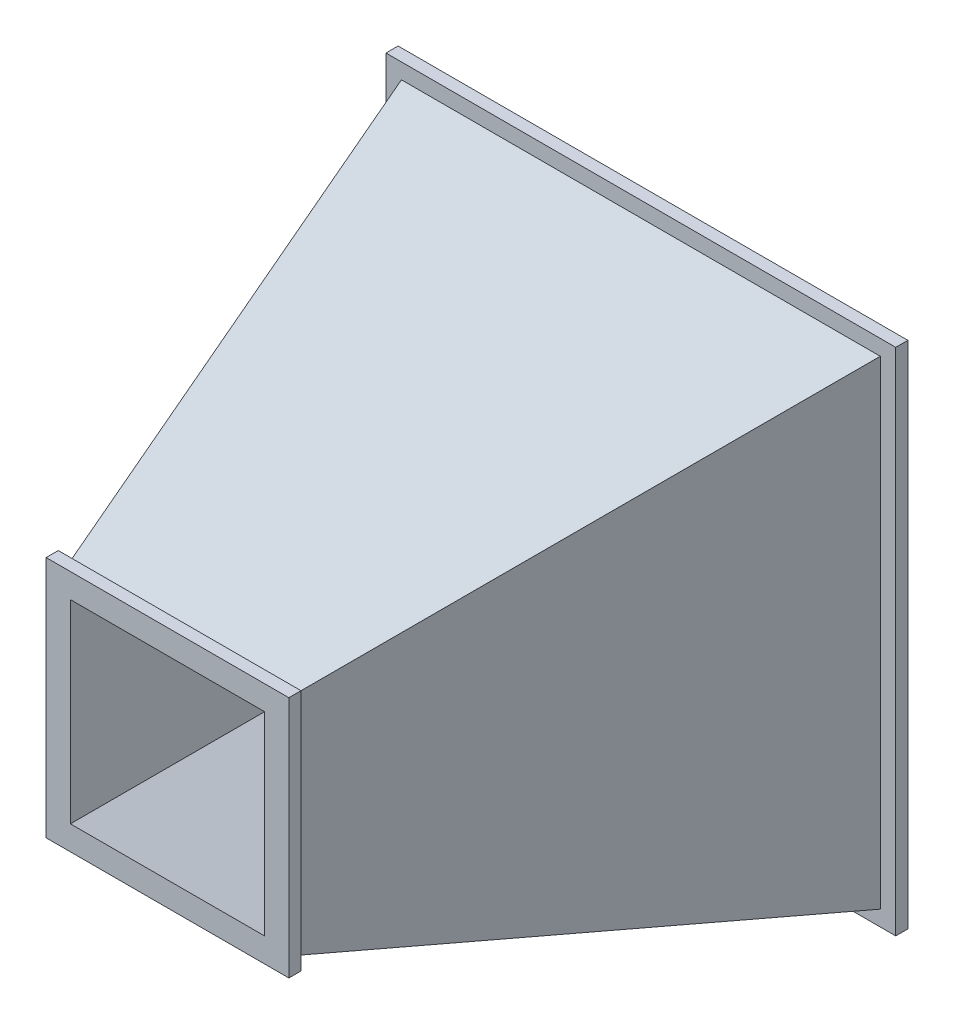
SolidWorks part; units mm, degrees
ref_plane "Front Plane" through (0, 0, 0) normal (0, 0, 1) x (1, 0, 0)
ref_plane "Top Plane" through (0, 0, 0) normal (0, 1, 0) x (1, 0, 0)
ref_plane "Right Plane" through (0, 0, 0) normal (1, 0, 0) x (0, 0, -1)
sketch "Sketch1" plane through (0, 0, 0) normal (0, 0, 1) x (1, 0, 0)
  line L1 (-100, 100) -> (100, 100)
  line L2 (-100, 100) -> (-100, -100)
  line L3 (-100, -100) -> (100, -100)
  line L4 (100, 100) -> (100, -100)
  line L5 (-100, 100) -> (100, -100) construction
  line L6 (-100, -100) -> (100, 100) construction
  point P0 (0, 0)
  dimension "D1" = 200
ref_plane "Plane1" through (0, 0, 200) normal (0, 0, 1) x (1, 0, 0)
sketch "Sketch2" plane through (0, 0, 200) normal (0, 0, 1) x (1, 0, 0)
  line L1 (-45, 45) -> (45, 45)
  line L2 (-45, 45) -> (-45, -45)
  line L3 (-45, -45) -> (45, -45)
  line L4 (45, 45) -> (45, -45)
  line L5 (-45, 45) -> (45, -45) construction
  line L6 (-45, -45) -> (45, 45) construction
  point P0 (0, 0)
  dimension "D1" = 90
  dimension "D2" = 90
loft "Loft2" add profiles "Sketch2", "Sketch1"
sketch "Sketch3" plane through (0, 0, 200) normal (0, 0, 1) x (1, 0, 0)
  line L8 (40, -40) -> (40, 40)
  line L9 (40, 40) -> (-40, 40)
  line L10 (-40, 40) -> (-40, -40)
  line L11 (-40, -40) -> (40, -40)
  line L12 (40, -40) -> (40, 40)
  line L13 (40, 40) -> (-40, 40)
  line L14 (-40, 40) -> (-40, -40)
  line L15 (-40, -40) -> (40, -40)
  dimension "D1" = 5
sketch "Sketch4" plane through (0, 0, 0) normal (0, 0, -1) x (-1, 0, 0)
  line L8 (-95, 95) -> (-95, -95)
  line L9 (-95, -95) -> (95, -95)
  line L10 (95, -95) -> (95, 95)
  line L11 (95, 95) -> (-95, 95)
  line L12 (-95, 95) -> (-95, -95)
  line L13 (-95, -95) -> (95, -95)
  line L14 (95, -95) -> (95, 95)
  line L15 (95, 95) -> (-95, 95)
  dimension "D1" = 5
sketch "Sketch5" plane through (0, 0, 200) normal (0, 0, 1) x (1, 0, 0)
  line L8 (50, -50) -> (50, 50)
  line L9 (50, 50) -> (-50, 50)
  line L10 (-50, 50) -> (-50, -50)
  line L11 (-50, -50) -> (50, -50)
  line L12 (50, -50) -> (50, 50)
  line L13 (50, 50) -> (-50, 50)
  line L14 (-50, 50) -> (-50, -50)
  line L15 (-50, -50) -> (50, -50)
  dimension "D1" = 5
sketch "Sketch6" plane through (0, 0, 0) normal (0, 0, -1) x (-1, 0, 0)
  line L8 (-105, 105) -> (-105, -105)
  line L9 (-105, -105) -> (105, -105)
  line L10 (105, -105) -> (105, 105)
  line L11 (105, 105) -> (-105, 105)
  line L12 (-105, 105) -> (-105, -105)
  line L13 (-105, -105) -> (105, -105)
  line L14 (105, -105) -> (105, 105)
  line L15 (105, 105) -> (-105, 105)
  dimension "D1" = 5
extrude "Boss-Extrude1" add sketch "Sketch6" against normal blind 5
extrude "Boss-Extrude2" add sketch "Sketch5" against normal blind 5 contours L13 L14 L15 L12
loft "Cut-Loft2" cut profiles "Sketch3", "Sketch4"
